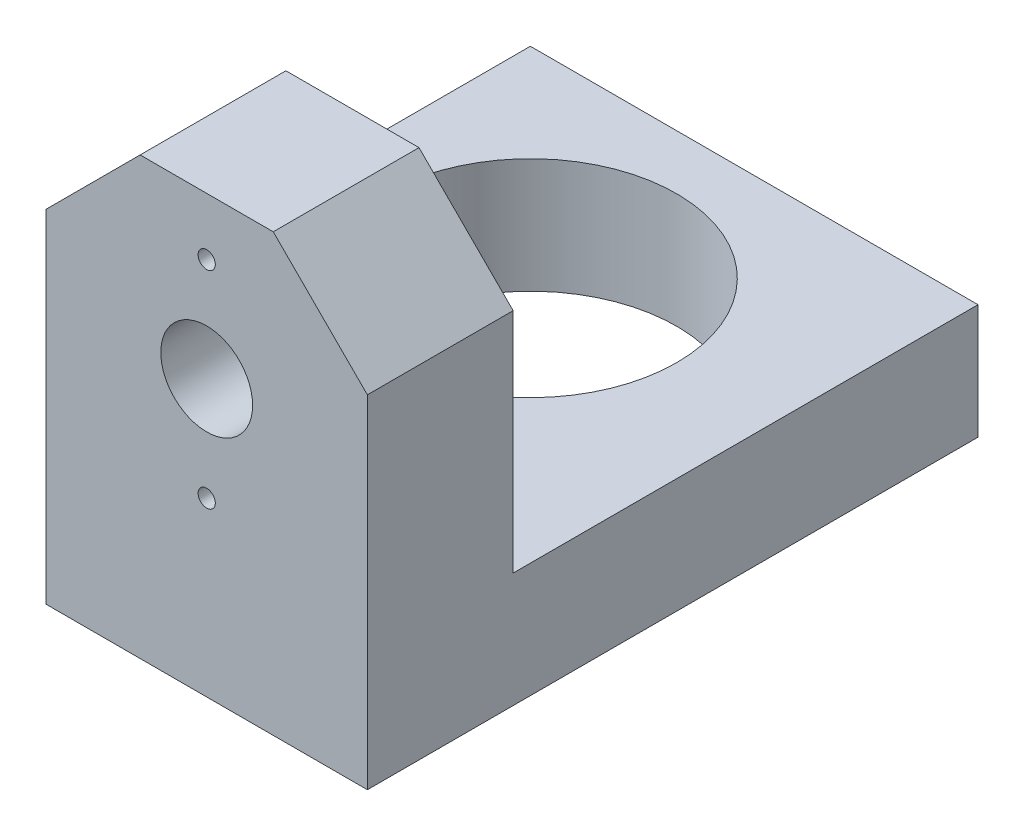
SolidWorks part; units mm, degrees
ref_plane "Front Plane" through (0, 0, 0) normal (0, 0, 1) x (1, 0, 0)
ref_plane "Top Plane" through (0, 0, 0) normal (0, 1, 0) x (1, 0, 0)
ref_plane "Right Plane" through (0, 0, 0) normal (1, 0, 0) x (0, 0, -1)
sketch "Sketch1" plane through (0, 0, 0) normal (0, 0, 1) x (1, 0, 0)
  line L0 (-5.799, 14) -> (5.799, 14)
  line L1 (5.799, 14) -> (14, 5.799)
  line L2 (14, 5.799) -> (14, -5.799)
  line L3 (14, -5.799) -> (5.799, -14) construction
  line L4 (5.799, -14) -> (-5.799, -14)
  line L5 (-5.799, -14) -> (-14, -5.799) construction
  line L6 (-14, -5.799) -> (-14, 5.799)
  line L7 (-14, 5.799) -> (-5.799, 14)
  line L8 (-14, -5.799) -> (-14, -14)
  line L9 (-14, -14) -> (-5.799, -14)
  line L10 (5.799, -14) -> (14, -14)
  line L11 (14, -14) -> (14, -5.799)
  circle A0 centre (0, 0) radius 4
  circle A1 centre (0, 9) radius 0.75
  circle A2 centre (0, -9) radius 0.75
  point P5 (0, 14)
  point P12 (0, -14)
  point P13 (-14, 0)
  point P14 (14, 0)
  dimension "D1" = 8
  dimension "D4" = 1.5
  dimension "D2" = 45
  dimension "D3" = 14
  dimension "D5" = 9
  dimension "D6" = 9
extrude "Boss-Extrude1" add sketch "Sketch1" along normal blind 12.7
sketch "Sketch2" plane through (0, -14, 0) normal (0, -1, 0) x (1, 0, 0)
  line L3 (14, 12.7) -> (-14, 12.7)
  line L4 (-14, 0) -> (-14, 12.7)
  line L5 (-14, 12.7) -> (14, 12.7) construction
  line L6 (-25, -40.5) -> (-25, -11)
  line L7 (-14, 0) -> (14, 0) construction
  line L8 (-14, 12.7) -> (-14, 0) construction
  line L12 (14, -40.5) -> (-25, -40.5)
  line L14 (14, -40.5) -> (14, 12.7)
  line L15 (14, 12.7) -> (14, 0) construction
  line L16 (-14, 0) -> (-25, -11)
  circle A1 centre (-7.5, -23) radius 12.75
  point P11 (0, 0)
  point P14 (0, 0)
  dimension "D1" = 25.5
  dimension "D3" = 17.5
  dimension "D2" = 17.5
  dimension "D4" = 23
  dimension "D5" = 7.5
  dimension "D6" = 45
extrude "Boss-Extrude2" add sketch "Sketch2" along normal blind 10 contours L6 L16 L4 L3 L14 L12 | A1
